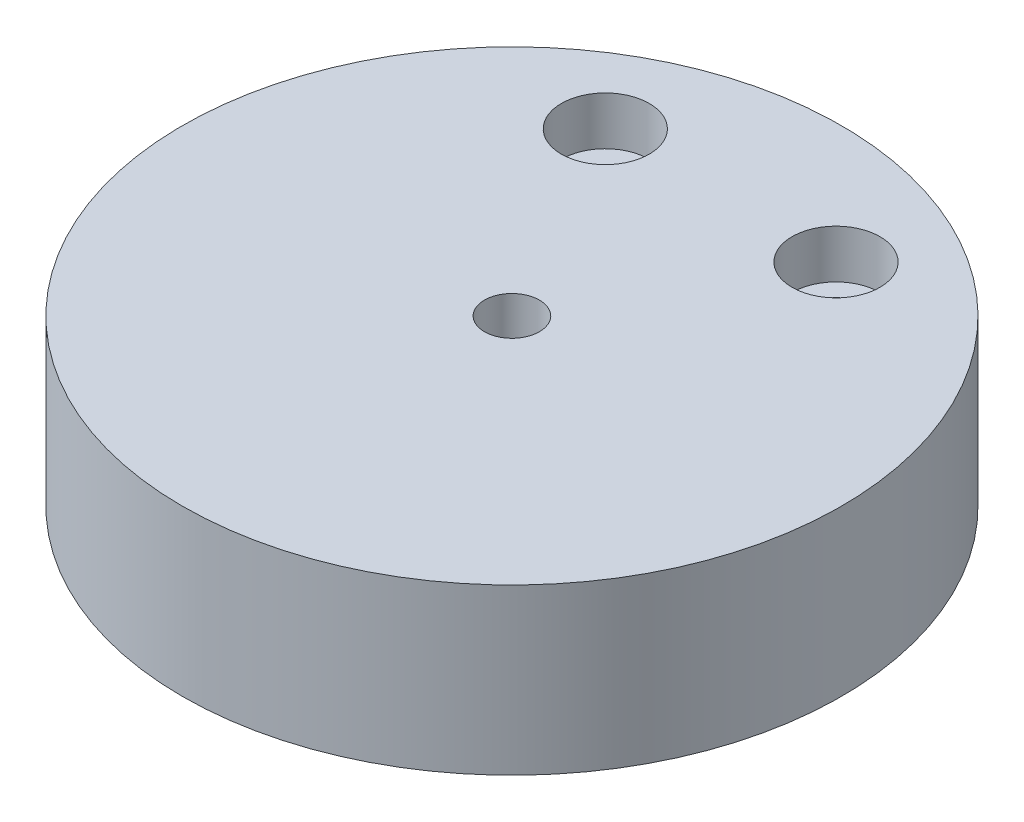
SolidWorks part; units mm, degrees
ref_plane "Front Plane" through (0, 0, 0) normal (0, 0, 1) x (1, 0, 0)
ref_plane "Top Plane" through (0, 0, 0) normal (0, 1, 0) x (1, 0, 0)
ref_plane "Right Plane" through (0, 0, 0) normal (1, 0, 0) x (0, 0, -1)
sketch "Sketch9" plane through (0, 0, 0) normal (0, 1, 0) x (1, 0, 0)
  line L0 (93.0887, 141.0799) -> (115.5887, 141.0799) construction
  circle A0 centre (121.7221, 83.9358) radius 6.8074
  circle A1 centre (113.5011, 102.9358) radius 1.5056
  circle A2 centre (132.5011, 101.4333) radius 1.4477
  dimension "D2" = 19
  dimension "D3" = 19
  dimension "D1" = 22.5
sketch "Sketch1" plane through (0, 0, 0) normal (0, 1, 0) x (1, 0, 0)
  circle A0 centre (121.7221, 83.9358) radius 30
  point P6 (121.7221, 83.9358)
  dimension "D3" = 60
extrude "Boss-Extrude1" add sketch "Sketch1" along normal blind 15
sketch "Sketch10" plane through (0, 15, 0) normal (0, 1, 0) x (1, 0, 0)
  circle A0 centre (121.7221, 83.9358) radius 2.5
  dimension "D1" = 5
extrude "Cut-Extrude2" cut sketch "Sketch10" against normal blind 15
sketch "Sketch11" plane through (0, 15, 0) normal (0, 1, 0) x (1, 0, 0)
  line L0 (91.7221, 83.9358) -> (151.7221, 83.9358) construction
  line L1 (121.7221, 113.9358) -> (121.7221, 53.9358) construction
  circle A0 centre (121.7221, 83.9358) radius 30 construction
  point P7 (111.2221, 102.9358)
  point P8 (132.2221, 102.9358)
  dimension "D1" = 19
  dimension "D2" = 10.5
hole_wizard "CBORE for M4 Hex Socket Head Cap Screw3" positions "3DSketch4" profile "Sketch12" counterbore size "M4" standard "ISO" end condition up to next
sketch3d "3DSketch4"
  point P0 (132.2221, 15, -102.9358)
  point P3 (111.2221, 15, -102.9358)
sketch "Sketch12" plane through (132.2221, 15, -102.9358) normal (1, 0, 0) x (0, 0, 1)
  line L0 (0, 0) -> (0, 15)
  line L1 (0, 15) -> (2.25, 15)
  line L3 (2.25, 15) -> (2.25, 4.4)
  line L4 (2.25, 4.4) -> (4, 4.4)
  line L5 (4, 4.4) -> (4, 0)
  line L7 (4, 0) -> (0, 0)
  line L11 (0, -6.35) -> (0, 107.95) construction
  dimension "Thru Hole Dia." = 4.5
  dimension "Thru Hole Depth" = 15
  dimension "C'Bore Dia." = 8
  dimension "C'Bore Depth" = 4.4
